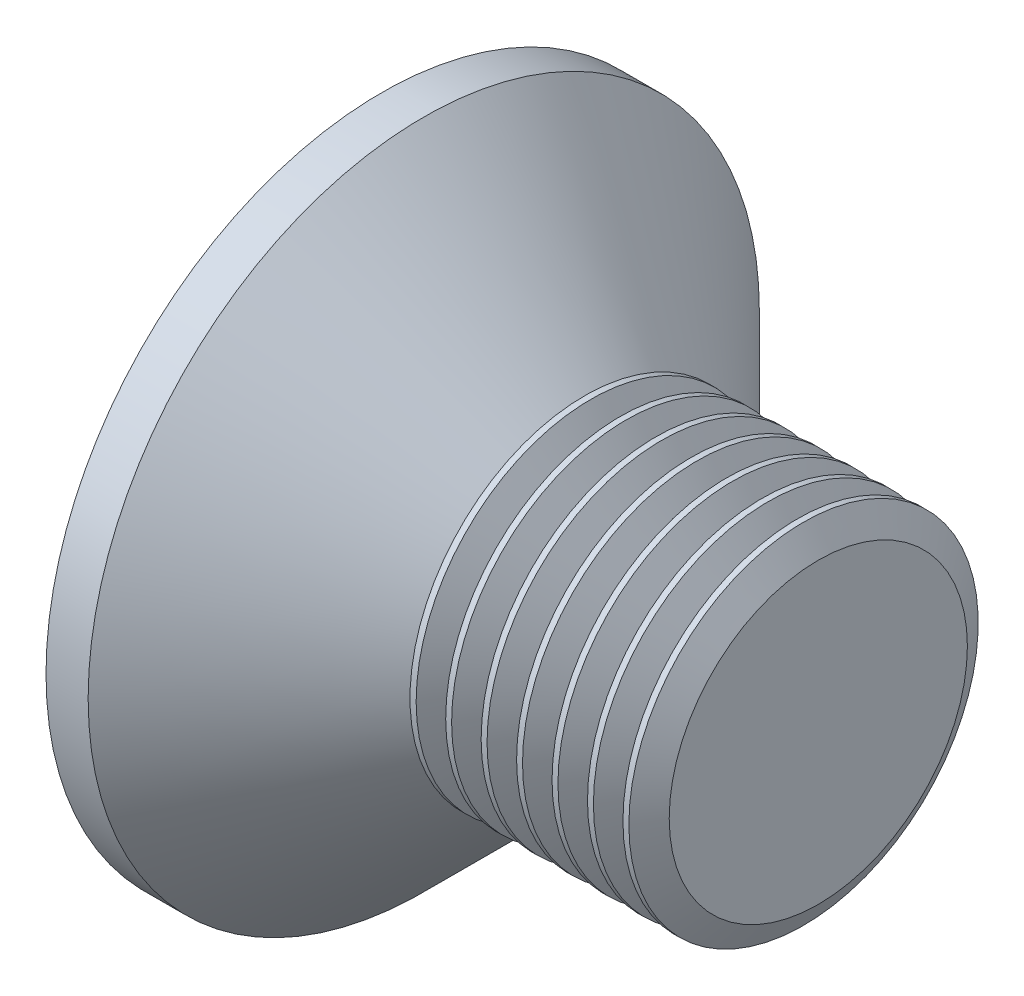
SolidWorks part; units mm, degrees
ref_plane "Front" through (0, 0, 0) normal (0, 0, 1) x (1, 0, 0)
ref_plane "Top" through (0, 0, 0) normal (0, 1, 0) x (1, 0, 0)
ref_plane "Right" through (0, 0, 0) normal (1, 0, 0) x (0, 0, -1)
sketch "Sketch1" plane through (0, 0, 0) normal (0, 0, 1) x (1, 0, 0)
  line L0 (10, 4) -> (7.15, 4)
  line L1 (7.15, 4) -> (4.65, 4)
  line L2 (4.65, 4) -> (0.965, 7.685)
  line L3 (0.965, 7.685) -> (0, 7.685)
  line L4 (10, 4) -> (10, 0)
  line L5 (4.5158, 0) -> (-89.8219, 0) construction
  line L6 (10, 0) -> (0, 0)
  line L7 (0, 7.685) -> (0, 0)
  dimension "D1" = 45
  dimension "d" = 8
  dimension "dk" = 15.37
  dimension "l" = 10
  dimension "k" = 4.65
  dimension "a" = 2.5
revolve "Base" add sketch "Sketch1" angle 360 about L5
cosmetic thread "ThreadCosmetic1" [suppressed] parameters "bb"=5.35, "THD_MINOR"=6.647
sketch "Sketch6" plane through (0, 0, 0) normal (1, 0, 0) x (0, 0, -1)
  line L0 (-1.9271, 0) -> (2.0512, 0) construction
  line L1 (0, 1.8651) -> (0, -2.0207) construction
  line L2 (0.89, 0.89) -> (0.89, 4.45)
  line L3 (0.89, 4.45) -> (-0.89, 4.45)
  line L4 (-0.89, 0.89) -> (-0.89, 4.45)
  line L5 (0.89, 0.89) -> (4.45, 0.89)
  line L6 (4.45, 0.89) -> (4.45, -0.89)
  line L7 (-4.45, 0.89) -> (-4.45, -0.89)
  line L8 (-0.89, 0.89) -> (-4.45, 0.89)
  line L9 (-0.89, -0.89) -> (-4.45, -0.89)
  line L10 (0.89, -0.89) -> (4.45, -0.89)
  line L11 (-0.89, -0.89) -> (-0.89, -4.45)
  line L12 (0.89, -4.45) -> (-0.89, -4.45)
  line L13 (0.89, -0.89) -> (0.89, -4.45)
  point P16 (-4.45, 0)
  point P17 (4.45, 0)
  dimension "D1" = 1.78
  dimension "m" = 8.9
extrude "CrossRecess" cut sketch "Sketch6" along normal blind 2.325
draft "Draft9" type of draft neutral plane draft angle 30 faces to draft 4 face at (1.1625, 4.45, 0) face at (1.1625, 0, 4.45) face at (1.1625, -4.45, 0) face at (1.1625, 0, -4.45) neutral plane through (0, 7.685, 0) neutral plane normal (-1, 0, 0) parameters "D1"=30
fillet "Fillet5" radius 0.3 4 edges at (1.1625, -0.89, -0.89) (1.1625, 0.89, -0.89) (1.1625, 0.89, 0.89) (1.1625, -0.89, 0.89)
sketch "Sketch7" plane through (0, 0, 0) normal (1, 0, 0) x (0, 0, -1)
  line L0 (-2.0126, 0) -> (1.9757, 0) construction
  line L1 (0, 1.9314) -> (0, -2.0126) construction
  line L2 (0, 0) -> (1.5555, 1.5555) construction
  line L3 (0, 1.3299) -> (3.1466, 3.1466)
  line L4 (-1.5402, 1.5402) -> (0, 0) construction
  line L5 (1.3299, 0) -> (3.1466, 3.1466)
  line L6 (0, -1.3299) -> (3.1466, -3.1466)
  line L7 (1.3299, 0) -> (3.1466, -3.1466)
  line L8 (-1.3299, 0) -> (-3.1466, -3.1466)
  line L9 (0, -1.3299) -> (-3.1466, -3.1466)
  line L10 (-1.3299, 0) -> (-3.1466, 3.1466)
  line L11 (0, 1.3299) -> (-3.1466, 3.1466)
  dimension "D3" = 15
extrude "Cut-Extrude3" [suppressed] cut sketch "Sketch7" along normal blind 10 draft 20
sketch "Sketch8" plane through (0, 0, 0) normal (0, 0, 1) x (1, 0, 0)
  line L0 (-28, 4.6765) -> (-31.2, 4)
  line L1 (-31.2, 4) -> (4.65, 4)
  line L3 (10, -4) -> (10, 4) construction
  line L6 (4.65, 4) -> (4.65, 9)
  line L7 (4.65, 9) -> (-28, 9)
  line L8 (-28, 9) -> (-28, 4.6765)
  line L9 (62.4753, 0.6765) -> (52.9594, 0.6765) construction
  dimension "D1" = 5
  dimension "x" = 3.2
  dimension "b" = 38
sketch "Sketch9" plane through (0, 0, 0) normal (0, 0, 1) x (1, 0, 0)
  line L0 (10, 3.4141) -> (10.3382, 4)
  line L1 (10.3382, 4) -> (10.3382, 4.6765)
  line L2 (10.3382, 4.6765) -> (9.6617, 4.6765)
  line L3 (9.6617, 4.6765) -> (9.6617, 4)
  line L4 (9.6617, 4) -> (10, 3.4141)
  line L5 (0, 0) -> (73.843, 0) construction
  line L6 (10, -4) -> (10, 4) construction
  dimension "D1" = 8
  dimension "D2" = 0.6765
revolve "Cut-Revolve10" cut sketch "Sketch9" angle 360 about L5
pattern_linear "LPattern10" count 7 spacing 0.8118 along (-1, 0, 0) of "Cut-Revolve10"
equation "\"D1@Sketch6\" = \"m@Sketch6\" / 5"
equation "\"D1@CrossRecess\" = \"k@Sketch1\" / 2"
equation "\"D1@Sketch9\" = \"d@Sketch1\""
equation "\"D2@Sketch9\" =  ( \"d@Sketch1\" - \"THD_MINOR@ThreadCosmetic1\" )  / 2"
equation "\"D3@LPattern10\" = \"D2@Sketch9\" * 1.2"
equation "\"D1@LPattern10\" = \"bb@ThreadCosmetic1\" / \"D3@LPattern10\" "
